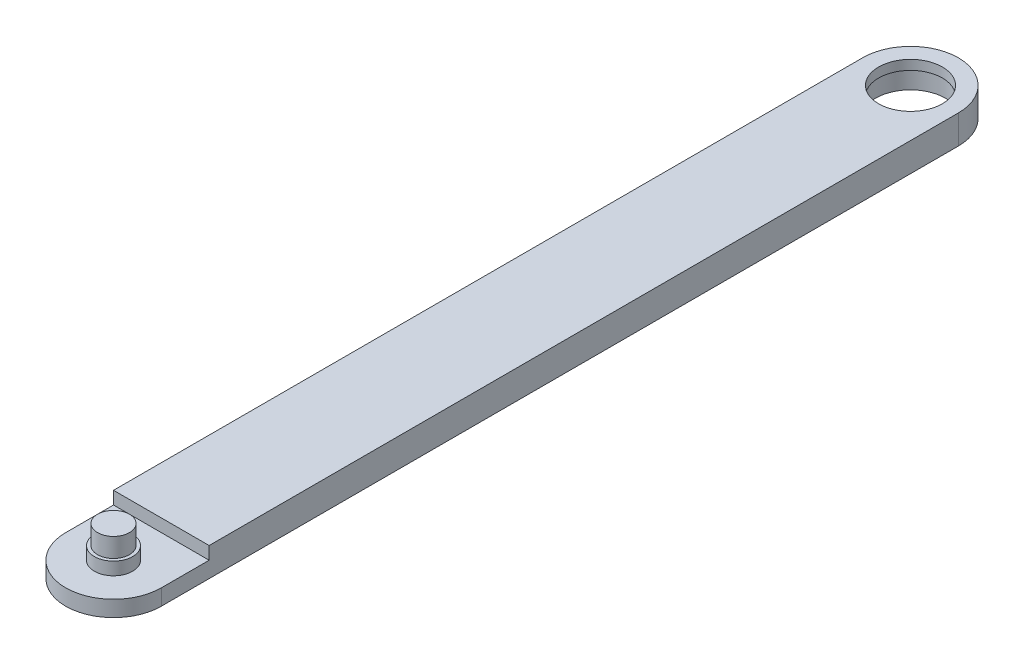
SolidWorks part; units mm, degrees
ref_plane "정면" through (0, 0, 0) normal (0, 0, 1) x (1, 0, 0)
ref_plane "윗면" through (0, 0, 0) normal (0, 1, 0) x (1, 0, 0)
ref_plane "우측면" through (0, 0, 0) normal (1, 0, 0) x (0, 0, -1)
sketch "스케치1" plane through (0, 0, 0) normal (0, 1, 0) x (1, 0, 0)
  circle A0 centre (0, 0) radius 6
  dimension "D1" = 12
extrude "보스-돌출1" add sketch "스케치1" along normal blind 1
sketch "스케치2" plane through (0, 1, 0) normal (0, 1, 0) x (1, 0, 0)
  line L0 (-15, 0) -> (-15, -250)
  line L1 (0, 0) -> (0, -250) construction
  line L2 (15, -250) -> (15, 0)
  arc A0 (15, 0) -> (-15, 0) centre (0, 0) ccw
  arc A1 (-15, -250) -> (15, -250) centre (0, -250) ccw
  dimension "D1" = 30
  dimension "D2" = 30
  dimension "D3" = 250
extrude "보스-돌출2" add sketch "스케치2" along normal blind 9
sketch "스케치8" plane through (0, 10, 0) normal (0, 1, 0) x (1, 0, 0)
  line L0 (-15, 0) -> (-15, -250) construction
  line L1 (-15, -265) -> (15, -265)
  line L2 (-15, -265) -> (-15, -235)
  line L3 (-15, -235) -> (15, -235)
  line L4 (15, -265) -> (15, -235)
  line L5 (15, -250) -> (15, 0) construction
  arc A0 (-15, -250) -> (15, -250) centre (0, -250) ccw construction
  dimension "D1" = 15
  dimension "D2" = 30
extrude "컷-돌출2" cut sketch "스케치8" against normal blind 4
sketch "스케치9" plane through (0, 6, 0) normal (0, 1, 0) x (1, 0, 0)
  circle A0 centre (0, -250) radius 6
  arc A1 (-15, -250) -> (15, -250) centre (0, -250) ccw construction
  dimension "D1" = 12
extrude "보스-돌출6" add sketch "스케치9" along normal blind 4
sketch "스케치10" plane through (0, 10, 0) normal (0, 1, 0) x (1, 0, 0)
  circle A0 centre (0, -250) radius 5
  dimension "D1" = 10
extrude "보스-돌출7" add sketch "스케치10" along normal blind 6
sketch "스케치11" plane through (0, 0, 0) normal (0, -1, 0) x (1, 0, 0)
  circle A0 centre (0, 0) radius 11
  dimension "D1" = 22
extrude "컷-돌출3" cut sketch "스케치11" against normal blind 7
sketch "스케치12" plane through (0, 7, 0) normal (0, -1, 0) x (1, 0, 0)
  circle A0 centre (0, 0) radius 10
  dimension "D1" = 20
extrude "컷-돌출4" cut sketch "스케치12" against normal through all
